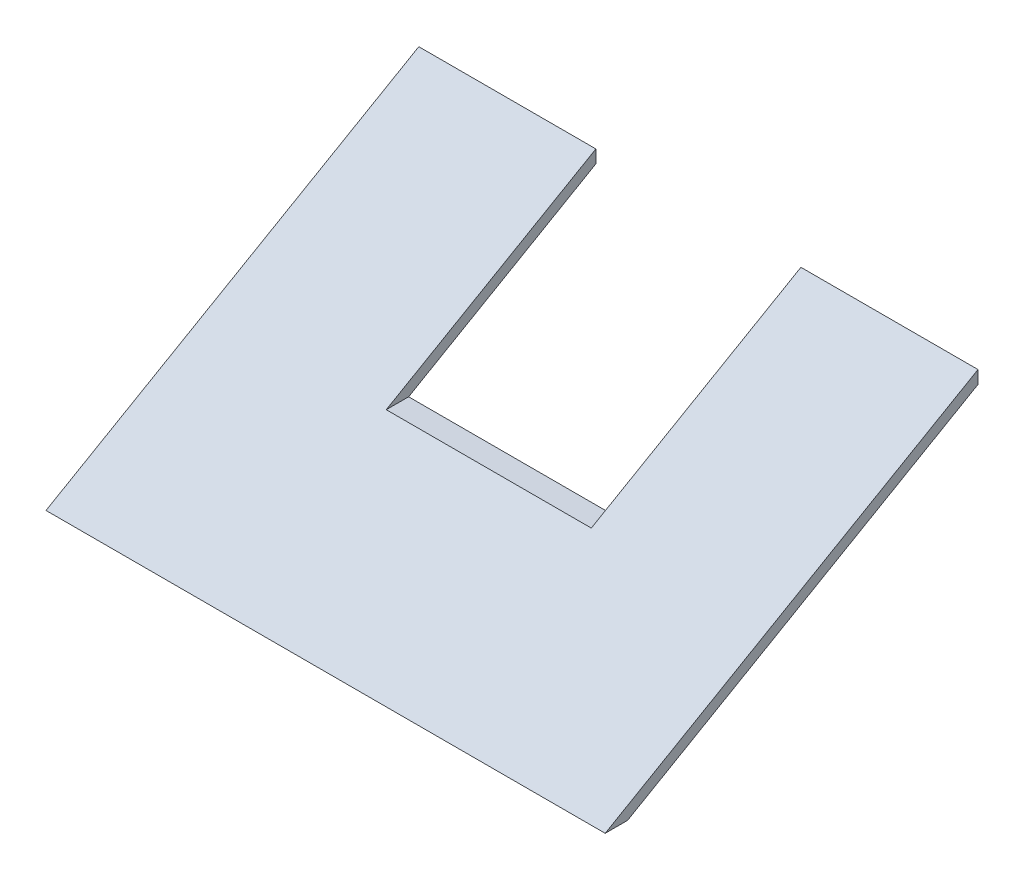
SolidWorks part; units mm, degrees
ref_plane "Front Plane" through (0, 0, 0) normal (0, 0, 1) x (1, 0, 0)
ref_plane "Top Plane" through (0, 0, 0) normal (0, 1, 0) x (1, 0, 0)
ref_plane "Right Plane" through (0, 0, 0) normal (1, 0, 0) x (0, 0, -1)
sketch "Sketch1" plane through (0, 0, 0) normal (1, 0, 0) x (0, 0, -1)
  line L0 (0, 0) -> (-94, -54.2709)
  line L1 (-94, -54.2709) -> (-100, -54.2709)
  line L2 (-100, -54.2709) -> (0, 3.4641)
  line L3 (0, 3.4641) -> (0, 0)
  dimension "D1" = 100
  dimension "D2" = 30
  dimension "D3" = 3
extrude "Boss-Extrude1" add sketch "Sketch1" along normal blind 150
sketch "Sketch2" plane through (0, 0, 0) normal (0, 0, 1) x (1, 0, 0)
  line L1 (102.5, 0) -> (47.5, 0) construction
  line L2 (102.5, 0) -> (102.5, -29)
  line L3 (102.5, -29) -> (47.5, -29)
  line L4 (47.5, 0) -> (47.5, -29)
  line L5 (150, 0) -> (0, 0) construction
  line L6 (47.5, 0) -> (47.5, 3.4641)
  line L7 (150, 3.4641) -> (0, 3.4641) construction
  line L8 (47.5, 3.4641) -> (102.5, 3.4641)
  line L9 (102.5, 3.4641) -> (102.5, 0)
  point P9 (75, 0)
  point P12 (75, 0)
  dimension "D1" = 55
  dimension "D2" = 29
extrude "Cut-Extrude1" cut sketch "Sketch2" along normal through all
